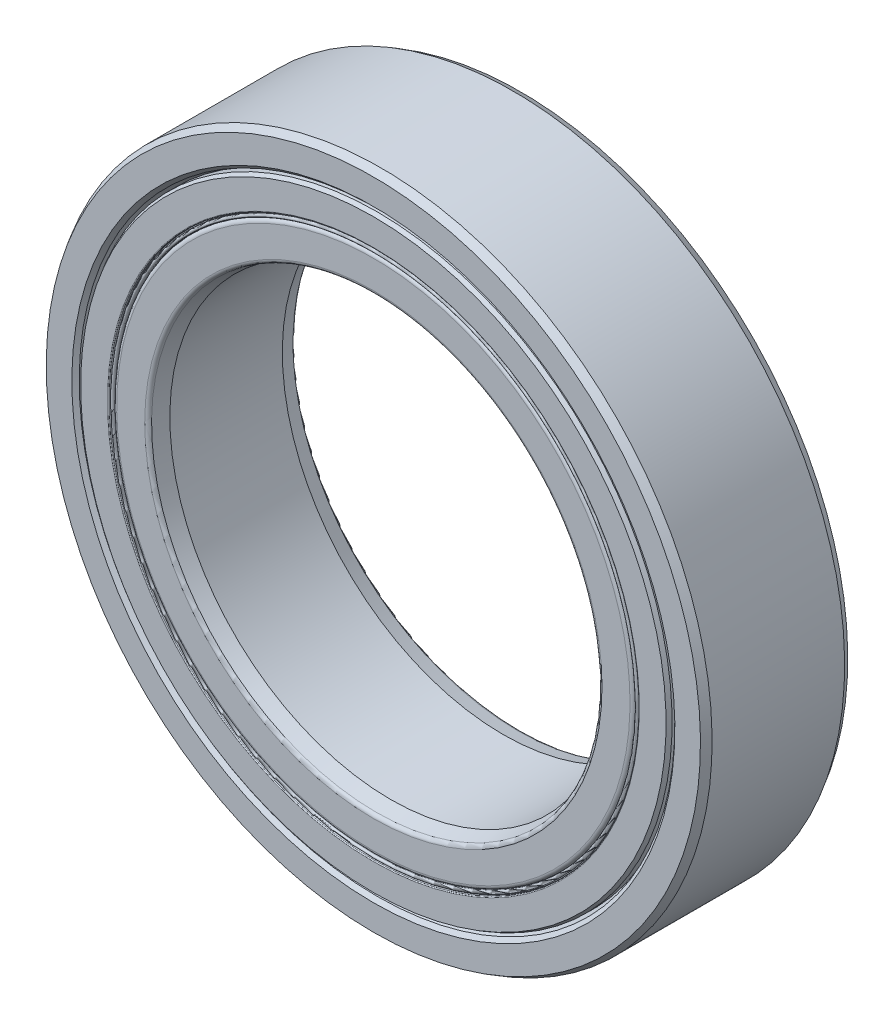
SolidWorks part; units mm, degrees
ref_plane "Front Plane" through (0, 0, 0) normal (0, 0, 1) x (1, 0, 0)
ref_plane "Top Plane" through (0, 0, 0) normal (0, 1, 0) x (1, 0, 0)
ref_plane "Right Plane" through (0, 0, 0) normal (1, 0, 0) x (0, 0, -1)
sketch "Sketch1" plane through (0, 0, 0) normal (0, 0, 1) x (1, 0, 0)
  line L0 (-9, 0) -> (9, 0) construction
  line L1 (-6, 0) -> (6, 0) construction
  circle A0 centre (0, 0) radius 6 construction
  circle A1 centre (0, 0) radius 9 construction
  point P3 (0, 0)
  point P6 (0, 0)
  point P7 (0, -6)
  point P11 (0, -9)
  point P12 (0, 6)
  point P13 (0, 9)
  dimension "OD" = 18
  dimension "ID" = 12
sketch "Sketch2" plane through (0, 0, 0) normal (1, 0, 0) x (0, 0, -1)
  line L0 (-2, 9) -> (2, 9) construction
  line L1 (0, 9) -> (0, -9) construction
  line L2 (1.8, 9) -> (-1.8, 9)
  line L3 (-1.8, 9) -> (-2, 8.8845)
  line L4 (-2, 8.8845) -> (-2, 8.189)
  line L5 (-1.683, 8.01) -> (-1.0244, 8.01)
  line L6 (1.683, 8.01) -> (1.0244, 8.01)
  line L7 (2, 8.8845) -> (2, 8.189)
  line L8 (1.8, 9) -> (2, 8.8845)
  line L9 (-1.0244, 8.01) -> (-1.0244, 8.34) construction
  line L10 (-1.0244, 8.34) -> (-1.0244, 8.67) construction
  line L11 (0, 9) -> (0, -9) construction
  line L12 (-2, 0) -> (2, 0) construction
  line L13 (2, 6) -> (-2, 6) construction
  line L14 (-2, 6) -> (-2, -6) construction
  line L15 (-2, -6) -> (2, -6) construction
  line L16 (2, 9) -> (2, -9) construction
  line L17 (-1.0244, 8.67) -> (-1.0244, 9) construction
  line L18 (-1.0244, 8.67) -> (0, 8.67) construction
  line L20 (-1.683, 8.01) -> (-1.9, 8.089)
  line L21 (-1.9, 8.089) -> (-2, 8.189)
  line L26 (1.9, 8.089) -> (2, 8.189)
  line L27 (1.683, 8.01) -> (1.9, 8.089)
  arc A0 (-1.0244, 8.01) -> (1.0244, 8.01) centre (0, 7.545) cw
  circle A1 centre (0, 7.545) radius 1.125 construction
  point P17 (0, 0)
  point P21 (0, 9)
  point P30 (0, -6)
  dimension "Approx. Ball Dia." = 2.25
  dimension "Width" = 4
  dimension "For Shaft Diameter" = 12
  dimension "For Housing ID" = 18
  dimension "D4" = 16.02
  dimension "D2" = 20
  dimension "D5" = 45
  dimension "D1" = 30
  dimension "D6" = 0.2
  dimension "D7" = 0.1
sketch "Sketch3" plane through (0, 0, 0) normal (1, 0, 0) x (0, 0, -1)
  line L14 (-1.683, 8.01) -> (-1.9, 8.089) construction
  line L15 (-1.9, 8.089) -> (-2, 8.189) construction
  line L16 (-2, 8.8845) -> (-2, 8.189) construction
  line L17 (-1.8, 9) -> (-2, 8.8845) construction
  line L18 (1.8, 9) -> (-1.8, 9) construction
  line L19 (1.8, 9) -> (2, 8.8845) construction
  line L20 (2, 8.8845) -> (2, 8.189) construction
  line L21 (1.9, 8.089) -> (2, 8.189) construction
  line L22 (1.683, 8.01) -> (1.9, 8.089) construction
  line L23 (1.683, 8.01) -> (1.0244, 8.01) construction
  line L24 (-1.683, 8.01) -> (-1.0244, 8.01) construction
  line L25 (-1.683, 8.01) -> (-1.9, 8.089)
  line L26 (-1.9, 8.089) -> (-2, 8.189)
  line L27 (-2, 8.8845) -> (-2, 8.189)
  line L28 (-1.8, 9) -> (-2, 8.8845)
  line L29 (1.8, 9) -> (-1.8, 9)
  line L30 (1.8, 9) -> (2, 8.8845)
  line L31 (2, 8.8845) -> (2, 8.189)
  line L32 (1.9, 8.089) -> (2, 8.189)
  line L33 (1.683, 8.01) -> (1.9, 8.089)
  line L34 (1.683, 8.01) -> (1.0244, 8.01)
  line L35 (-1.683, 8.01) -> (-1.0244, 8.01)
  arc A2 (1.0244, 8.01) -> (-1.0244, 8.01) centre (0, 7.545) ccw construction
  arc A3 (1.0244, 8.01) -> (-1.0244, 8.01) centre (0, 7.545) ccw
revolve "Revolve1" add sketch "Sketch3" angle 360 about L12
sketch "Sketch4" plane through (0, 0, 0) normal (1, 0, 0) x (0, 0, -1)
  line L0 (0, 9) -> (0, -9) construction
  line L1 (0, 9) -> (0, -9) construction
  line L2 (-1.5276, 6) -> (-1.9194, 6.105)
  line L3 (-2, 6.21) -> (-2, 6.9713)
  line L4 (2, -8.8845) -> (2, 8.8845) construction
  line L5 (-1.8913, 7.08) -> (-1.0244, 7.08)
  line L6 (-1.5276, 6) -> (1.5276, 6)
  line L7 (2, 8.8845) -> (2, 8.189) construction
  line L8 (1.5276, 6) -> (1.9194, 6.105)
  line L9 (0, 8.67) -> (0, 6) construction
  line L10 (2, 6.21) -> (2, 6.9713)
  line L11 (1.8913, 7.08) -> (1.0244, 7.08)
  line L12 (1.5276, 6) -> (1.5276, 6.105) construction
  line L13 (1.5276, 6.105) -> (1.5276, 6.21) construction
  line L14 (1.5276, 6.21) -> (1.5276, 6.315) construction
  line L15 (1.5276, 6.315) -> (1.5276, 6.42) construction
  circle A0 centre (0, 7.545) radius 1.125 construction
  arc A1 (1.0244, 7.08) -> (-1.0244, 7.08) centre (0, 7.545) cw
  arc A2 (2, 6.9713) -> (1.8913, 7.08) centre (1.8913, 6.9713) ccw
  arc A3 (-2, 6.9713) -> (-1.8913, 7.08) centre (-1.8913, 6.9713) cw
  arc A4 (1.9194, 6.105) -> (2, 6.21) centre (1.8913, 6.21) ccw
  arc A5 (-1.9194, 6.105) -> (-2, 6.21) centre (-1.8913, 6.21) cw
  point P14 (2, 6.1266)
  point P36 (0, 6.42)
  dimension "D1" = 15
revolve "Revolve2" add sketch "Sketch4" angle 360 about L12
sketch "Sketch5" plane through (0, 0, 0) normal (1, 0, 0) x (0, 0, -1)
  line L0 (-1.125, 7.545) -> (1.125, 7.545)
  arc A2 (-1.125, 7.545) -> (1.125, 7.545) centre (0, 7.545) cw
  arc A3 (1.0244, 8.01) -> (-1.0244, 8.01) centre (0, 7.545) ccw construction
revolve "Revolve3" add sketch "Sketch5" angle 360 about L0
pattern_circular "CirPattern1" count 14 over 360 about axis through (0, 0, 0) along (0, 0, 1) of bodies 104
sketch "Sketch6" plane through (0, 0, 0) normal (1, 0, 0) x (0, 0, -1)
  line L1 (-1.8961, 8.01) -> (-1.125, 8.01)
  line L2 (-2, 7.95) -> (-2, 7.224)
  line L3 (-1.976, 7.2) -> (-1.125, 7.2)
  line L4 (-1.125, 8.01) -> (-1.125, 7.2)
  line L5 (-2, 6.21) -> (-2, 6.9713) construction
  line L6 (-1.8, 9) -> (-2, 8.8845) construction
  line L7 (0, 9) -> (0, 6) construction
  line L8 (1.976, 7.2) -> (1.125, 7.2)
  line L9 (1.125, 8.01) -> (1.125, 7.2)
  line L10 (1.8961, 8.01) -> (1.125, 8.01)
  line L11 (2, 7.95) -> (2, 7.224)
  line L13 (-1.8913, 7.08) -> (-1.0244, 7.08) construction
  line L14 (-2, 7.95) -> (-1.8961, 8.01)
  line L15 (-1.683, 8.01) -> (-1.0244, 8.01) construction
  line L16 (2, 7.95) -> (1.8961, 8.01)
  arc A0 (-2, 7.224) -> (-1.976, 7.2) centre (-1.976, 7.224) ccw
  circle A1 centre (0, 7.545) radius 1.125 construction
  arc A2 (2, 7.224) -> (1.976, 7.2) centre (1.976, 7.224) cw
  point P26 (-2, 7.2)
  dimension "D3" = 0.024
  dimension "D1" = 0.12
  dimension "D2" = 0.06
revolve "Revolve4" add sketch "Sketch6" angle 360 about L12
sketch "Sketch7" plane through (0, 0, 0) normal (1, 0, 0) x (0, 0, -1)
  line L3 (-1.125, 7.2) -> (-1.9026, 7.2)
  line L4 (-1.976, 7.2) -> (-1.125, 7.2) construction
  line L7 (0, 6.42) -> (0, 6) construction
  line L8 (0, 9) -> (0, -9) construction
  line L21 (-1.9026, 7.2) -> (-1.9322, 7.1948)
  line L22 (-1.93, 7.17) -> (-1.955, 7.17)
  line L23 (-1.955, 7.08) -> (-1.125, 7.08)
  line L24 (-1.125, 7.08) -> (-1.125, 7.2)
  line L25 (-1.8913, 7.08) -> (-1.0244, 7.08) construction
  line L26 (-2, 7.224) -> (-2, 7.08) construction
  line L27 (-2, 7.08) -> (-1.955, 7.08) construction
  line L28 (-1.9026, 7.2) -> (-1.9026, 7.17) construction
  line L29 (-1.9026, 7.17) -> (-1.9026, 7.14) construction
  line L30 (-1.9026, 7.14) -> (-1.9026, 7.11) construction
  line L31 (-1.9026, 7.11) -> (-1.9026, 7.08) construction
  circle A2 centre (0, 7.545) radius 1.125 construction
  arc A9 (-1.9322, 7.1948) -> (-1.93, 7.17) centre (-1.93, 7.1825) ccw
  arc A10 (-1.955, 7.17) -> (-1.955, 7.08) centre (-1.955, 7.125) ccw
  dimension "D1" = 0.025
  dimension "D2" = 10
revolve "Revolve5" add sketch "Sketch7" angle 360 about L12
equation "\"D4@Sketch2\"=\"OD@Sketch1\"*.89"
equation "\"D1@Sketch6\"=(\"OD@Sketch1\"-\"ID@Sketch1\")*.02"
equation "\"D2@Sketch6\"=\"D1@Sketch6\"*.5"
equation "\"D3@Sketch6\"=\"D1@Sketch6\"*.2"
equation "\"D6@Sketch2\"=\"Width@Sketch2\"*.05"
equation "\"D7@Sketch2\"=\"D6@Sketch2\"*.5"
equation "\"D1@CirPattern1\" =  ( pi * \"OD@Sketch1\" )  * .5625 / \"Approx. Ball Dia.@Sketch2\""
equation "\"Approx. Ball Dia.@Sketch2\"=(\"OD@Sketch1\"-\"ID@Sketch1\")*.5*.75"
